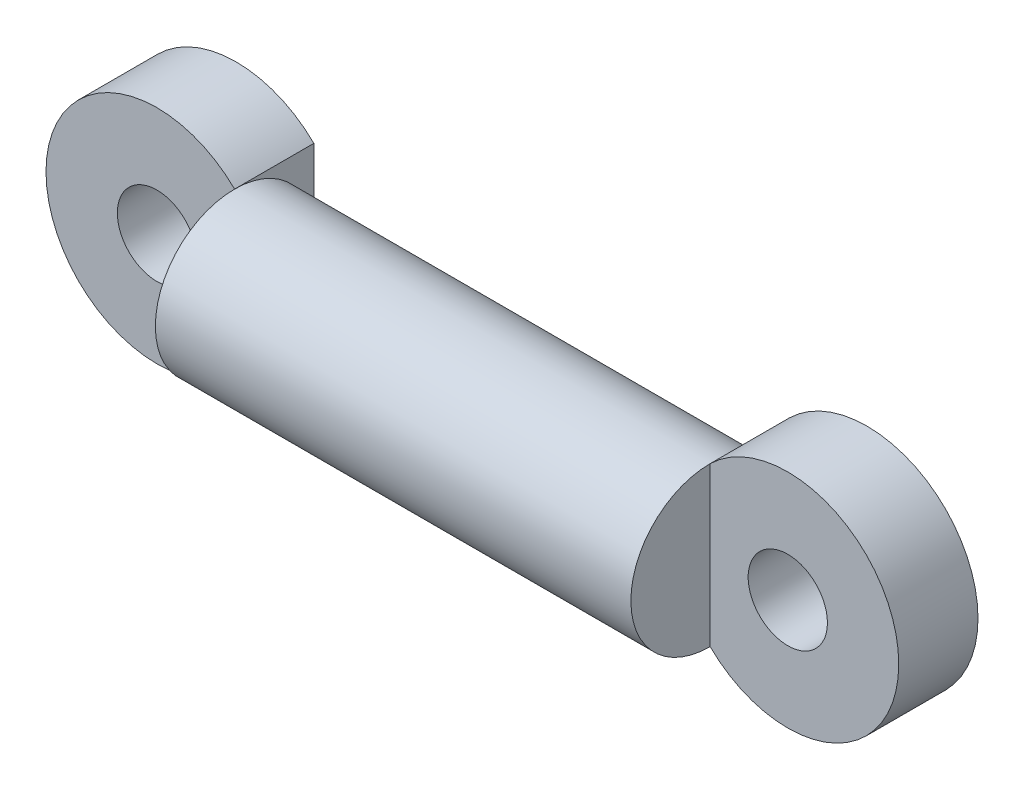
SolidWorks part; units mm, degrees
ref_plane "Front Plane" through (0, 0, 0) normal (0, 0, 1) x (1, 0, 0)
ref_plane "Top Plane" through (0, 0, 0) normal (0, 1, 0) x (1, 0, 0)
ref_plane "Right Plane" through (0, 0, 0) normal (1, 0, 0) x (0, 0, -1)
sketch "Sketch1" plane through (0, 0, 0) normal (0, 0, 1) x (1, 0, 0)
  line L0 (-15, 0) -> (15, 0)
  point P3 (0, 0)
  dimension "D1" = 30
revolve "Revolve-Thin1" add sketch "Sketch1" angle 360 about L0 wall 5
sketch "Sketch3" plane through (0, 0, 0) normal (0, 0, 1) x (1, 0, 0)
  line L0 (15, 5) -> (15, -5)
  line L1 (-15, -5) -> (-15, 5)
  arc A0 (15, 5) -> (15, -5) centre (19.899, 0) cw
  arc A1 (-15, 5) -> (-15, -5) centre (-19.899, 0) ccw
  circle A2 centre (-19.899, 0) radius 2.5
  circle A3 centre (19.899, 0) radius 2.5
  dimension "D1" = 7
  dimension "D2" = 5
extrude "Boss-Extrude2" add sketch "Sketch3" against normal blind 5
